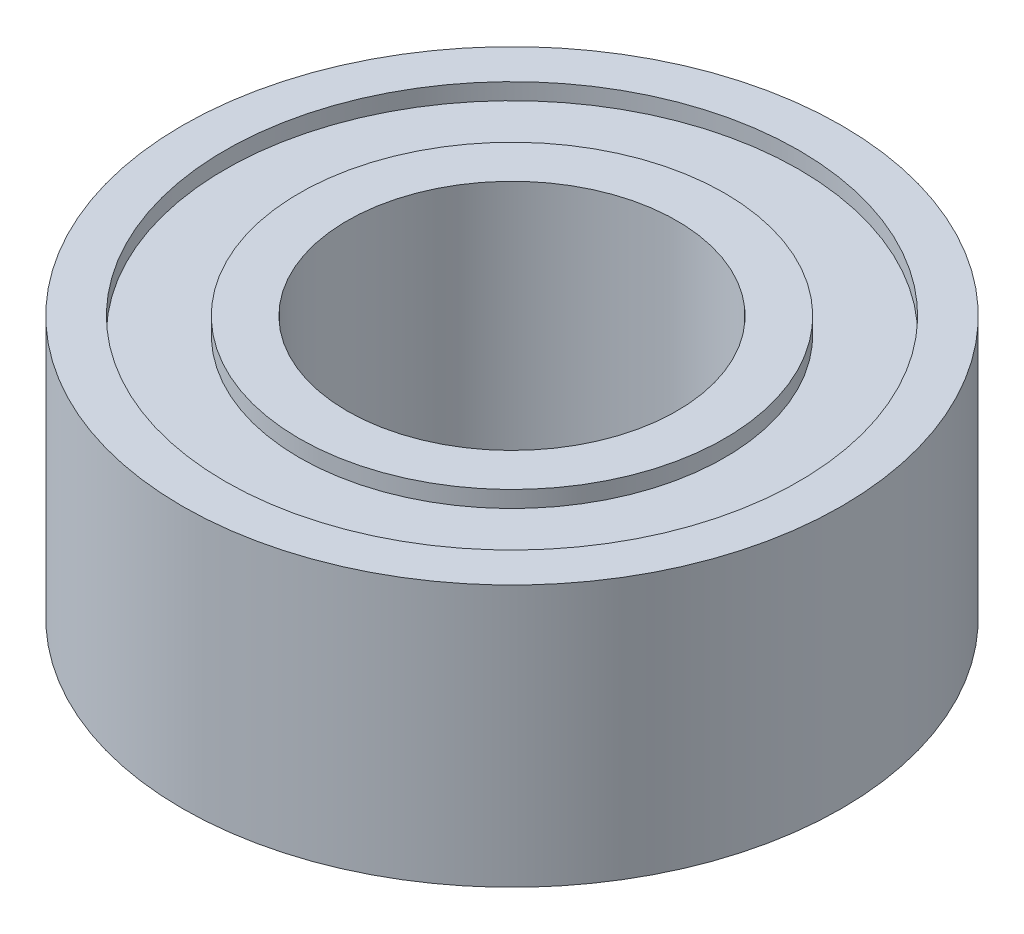
SolidWorks part; units mm, degrees
ref_plane "Front Plane" through (0, 0, 0) normal (0, 0, 1) x (1, 0, 0)
ref_plane "Top Plane" through (0, 0, 0) normal (0, 1, 0) x (1, 0, 0)
ref_plane "Right Plane" through (0, 0, 0) normal (1, 0, 0) x (0, 0, -1)
sketch "Sketch1" plane through (0, 0, 0) normal (0, 1, 0) x (1, 0, 0)
  circle A0 centre (0, 0) radius 5
  circle A1 centre (0, 0) radius 2.5
  dimension "D1" = 10
  dimension "D2" = 5
extrude "Boss-Extrude1" add sketch "Sketch1" along normal blind 3.97
sketch "Sketch2" plane through (0, 3.97, 0) normal (0, 1, 0) x (1, 0, 0)
  circle A0 centre (0, 0) radius 4.35
  circle A1 centre (0, 0) radius 3.225
  dimension "D1" = 8.7
  dimension "D2" = 6.45
extrude "Cut-Extrude1" cut sketch "Sketch2" against normal blind 0.25
sketch "Sketch3" plane through (0, 0, 0) normal (0, -1, 0) x (1, 0, 0)
  circle A0 centre (0, 0) radius 4.35
  circle A1 centre (0, 0) radius 3.225
  circle A2 centre (0, 0) radius 4.35 construction
  circle A3 centre (0, 0) radius 3.225 construction
extrude "Cut-Extrude2" cut sketch "Sketch3" against normal blind 0.25
